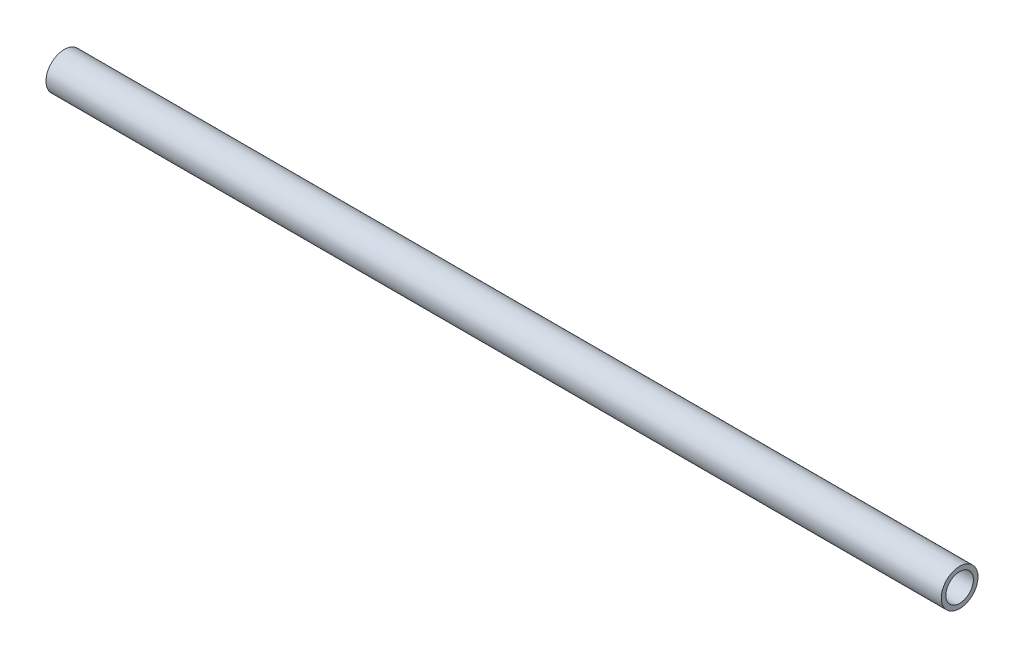
SolidWorks part; units mm, degrees
material "6061-T6 (SS)"
ref_plane "Front Plane" through (0, 0, 0) normal (0, 0, 1) x (1, 0, 0)
ref_plane "Top Plane" through (0, 0, 0) normal (0, 1, 0) x (1, 0, 0)
ref_plane "Right Plane" through (0, 0, 0) normal (1, 0, 0) x (0, 0, -1)
sketch "Sketch1" plane through (0, 0, 0) normal (1, 0, 0) x (0, 0, -1)
  circle A0 centre (0, 0) radius 12.7
  circle A1 centre (0, 0) radius 9.525
  point P5 (1.1182, 0)
  point P6 (1.278, 0)
  dimension "D1" = 25.4
  dimension "D2" = 3.175
extrude "Boss-Extrude1" add sketch "Sketch1" along normal mid plane 619.125
